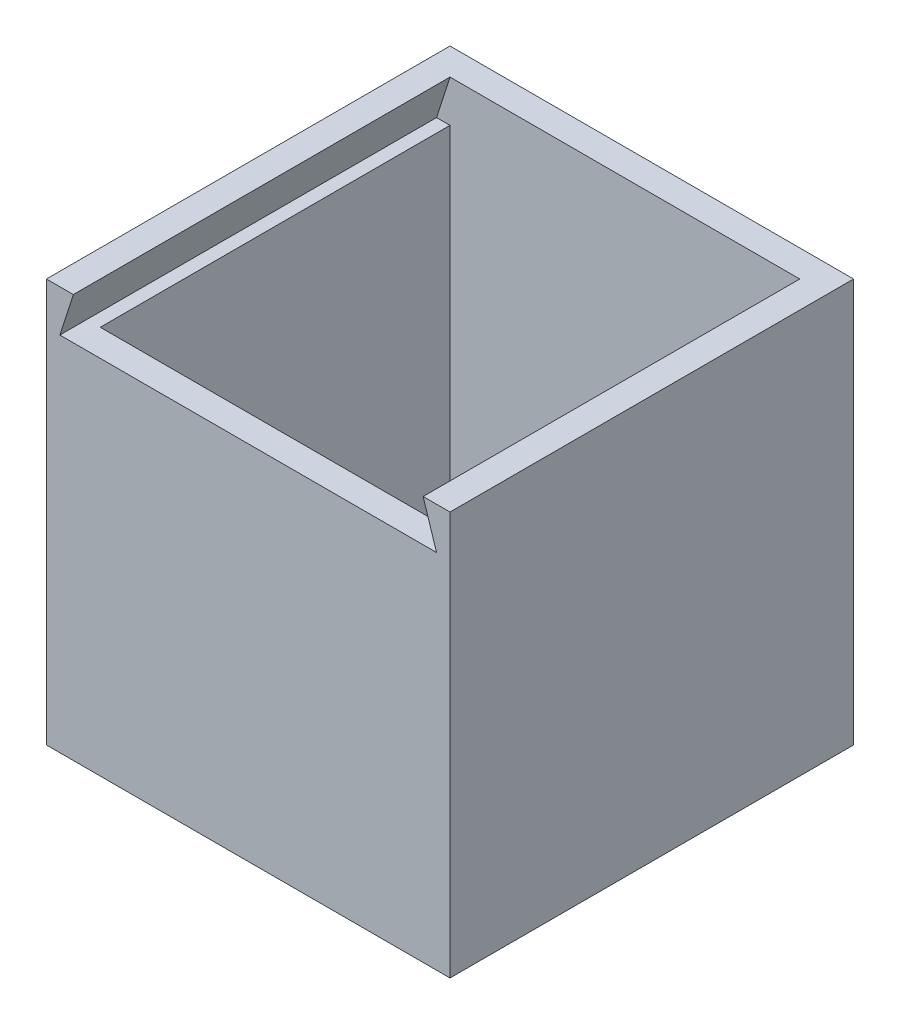
SolidWorks part; units mm, degrees
ref_plane "Front Plane" through (0, 0, 0) normal (0, 0, 1) x (1, 0, 0)
ref_plane "Top Plane" through (0, 0, 0) normal (0, 1, 0) x (1, 0, 0)
ref_plane "Right Plane" through (0, 0, 0) normal (1, 0, 0) x (0, 0, -1)
sketch "Sketch1" plane through (0, 0, 0) normal (0, 1, 0) x (1, 0, 0)
  line L1 (-47.8838, 26.1327) -> (47.3662, 26.1327)
  line L2 (-47.8838, 26.1327) -> (-47.8838, -69.1173)
  line L3 (-47.8838, -69.1173) -> (47.3662, -69.1173)
  line L4 (47.3662, 26.1327) -> (47.3662, -69.1173)
  dimension "D1" = 95.25
  dimension "D2" = 95.25
extrude "Boss-Extrude1" add sketch "Sketch1" along normal blind 95.25
shell "Shell1" thickness 6.35
sketch "Sketch2" plane through (0, 0, 69.1173) normal (0, 0, 1) x (1, 0, 0)
  line L0 (-47.8838, 95.25) -> (47.3662, 95.25) construction
  line L1 (-44.7088, 95.25) -> (44.1912, 95.25)
  line L2 (-44.7088, 95.25) -> (-44.7088, 85.3815)
  line L3 (-44.7088, 85.3815) -> (44.1912, 85.3815)
  line L4 (44.1912, 95.25) -> (44.1912, 85.3815)
  line L5 (-47.8838, 95.25) -> (-47.8838, 0) construction
  line L6 (47.3662, 95.25) -> (47.3662, 0) construction
  line L7 (-41.5338, 95.25) -> (-44.7088, 85.3815)
  line L8 (44.1912, 85.3815) -> (41.0162, 95.25)
  point P11 (0, 0)
  dimension "D1" = 3.175
  dimension "D2" = 3.175
  dimension "D3" = 3.175
  dimension "D4" = 3.175
extrude "Cut-Extrude1" cut sketch "Sketch2" against normal blind 88.9 contours L3 L8 L1 L7
sketch "Sketch3" plane through (0, 6.35, 0) normal (0, 1, 0) x (1, 0, 0)
  line L0 (-41.5338, 19.7827) -> (-41.5338, -62.7673) construction
  line L1 (-41.5338, 19.7827) -> (41.0162, 19.7827)
  line L2 (-41.5338, 19.7827) -> (-41.5338, 14.7827)
  line L3 (-41.5338, 14.7827) -> (41.0162, 14.7827)
  line L4 (41.0162, 19.7827) -> (41.0162, 14.7827)
  line L5 (-41.5338, 19.7827) -> (-41.5338, -69.1173) construction
  line L6 (41.0162, -69.1173) -> (41.0162, 19.7827) construction
  line L7 (41.0162, 19.7827) -> (-41.5338, 19.7827) construction
  dimension "D1" = 5
